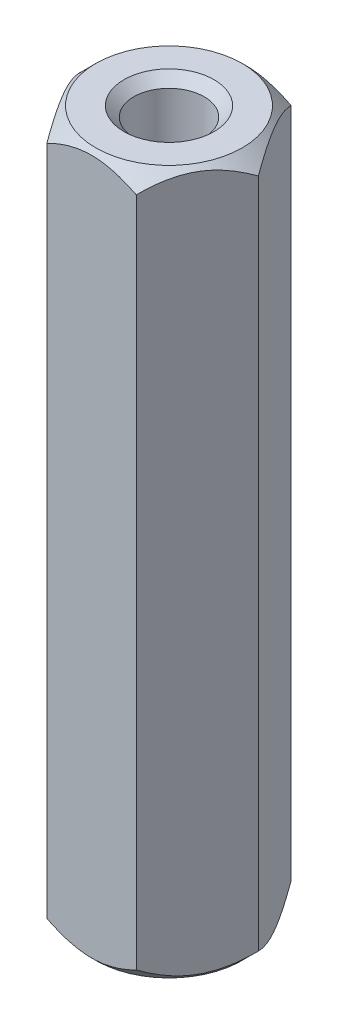
SolidWorks part; units mm, degrees
ref_plane "Front" through (0, 0, 0) normal (0, 0, 1) x (1, 0, 0)
ref_plane "Top" through (0, 0, 0) normal (0, 1, 0) x (1, 0, 0)
ref_plane "Right" through (0, 0, 0) normal (1, 0, 0) x (0, 0, -1)
sketch "Sketch1" plane through (0, 0, 0) normal (0, 1, 0) x (1, 0, 0)
  line L1 (1.5877, 2.75) -> (-1.5877, 2.75)
  line L2 (-1.5877, 2.75) -> (-3.1754, 0)
  line L3 (-3.1754, 0) -> (-1.5877, -2.75)
  line L4 (-1.5877, -2.75) -> (1.5877, -2.75)
  line L5 (1.5877, -2.75) -> (3.1754, 0)
  line L6 (3.1754, 0) -> (1.5877, 2.75)
  circle A0 centre (0, 0) radius 2.75 construction
  dimension "D1" = 5.5
extrude "Boss-Extrude1" add sketch "Sketch1" along normal blind 25
hole_wizard "M3 Tapped Hole1" positions "Sketch3" profile "Sketch2" tap size "M3" standard "ISO" end condition through all
sketch "Sketch3" plane through (0, 25, 0) normal (0, 1, 0) x (1, 0, 0)
  point P0 (0, 0)
sketch "Sketch2" plane through (0, 25, 0) normal (1, 0, 0) x (0, 0, 1)
  line L0 (0, 0) -> (0, 25)
  line L1 (0, 25) -> (1.6, 25)
  line L2 (1.25, 24.65) -> (1.25, 0.35)
  line L3 (1.25, 0.35) -> (1.6, 0)
  line L5 (1.6, 0) -> (0, 0)
  line L6 (-1.25, 0.35) -> (-1.6, 0) construction
  line L7 (1.6, 25) -> (1.25, 24.65)
  line L8 (-1.6, 25) -> (-1.25, 24.65) construction
  line L11 (0, -6.35) -> (0, 107.95) construction
  dimension "Thru Tap Drill Dia." = 2.5
  dimension "Thru Tap Drill Depth" = 25
  dimension "Near C'Sink Dia." = 3.2
  dimension "Near C'Sink Angle" = 90
  dimension "Far C'Sink Dia." = 3.2
  dimension "Far C'Sink Angle" = 90
cosmetic thread "Hole Thread1" parameters "D2"=3
sketch "Sketch4" plane through (0, 0, 0) normal (0, 0, 1) x (1, 0, 0)
  line L0 (0, 25) -> (0, 0) construction
  line L1 (-1.5877, 25) -> (1.5877, 25) construction
  line L2 (2.6, 0) -> (3.1754, 0.5754)
  line L3 (1.5877, 0) -> (3.1754, 0) construction
  line L4 (3.1754, 25) -> (3.1754, 0) construction
  line L5 (3.1754, 0.5754) -> (3.1754, 0)
  line L6 (3.1754, 0) -> (2.6, 0)
  line L7 (0, 12.5) -> (3.1754, 12.5) construction
  line L8 (3.1754, 25) -> (2.6, 25)
  line L9 (3.1754, 24.4246) -> (3.1754, 25)
  line L10 (2.6, 25) -> (3.1754, 24.4246)
  dimension "D1" = 5.2
  dimension "D2" = 45
revolve "Cut-Revolve1" cut sketch "Sketch4" angle 360 about L0
